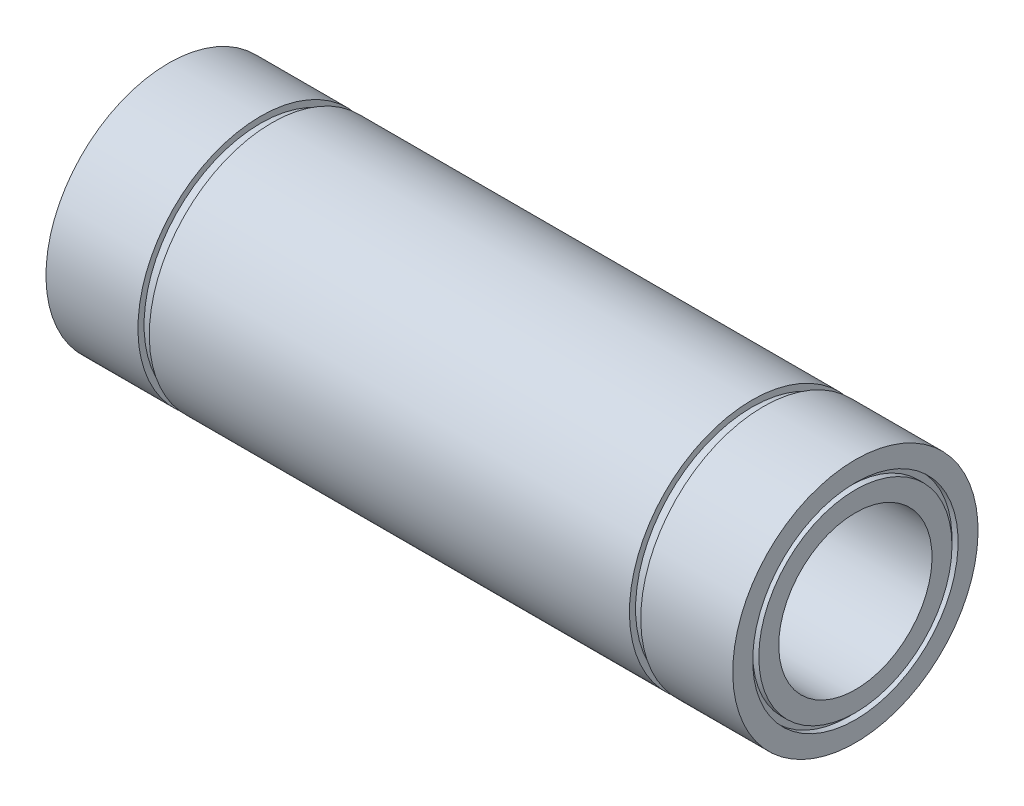
SolidWorks part; units mm, degrees
material "Ст3сп ГОСТ 535-2005"
ref_plane "Plano frontal" through (0, 0, 0) normal (0, 0, 1) x (1, 0, 0)
ref_plane "Plano superior" through (0, 0, 0) normal (0, 1, 0) x (1, 0, 0)
ref_plane "Plano direito" through (0, 0, 0) normal (1, 0, 0) x (0, 0, -1)
sketch "Esboço1" plane through (0, 0, 0) normal (0, 0, 1) x (1, 0, 0)
  line L0 (-56, 20) -> (-41, 20)
  line L1 (-41, 20) -> (-41, 19)
  line L2 (-41, 19) -> (-39.15, 19)
  line L3 (-39.15, 19) -> (-39.15, 20)
  line L4 (-39.15, 20) -> (39.15, 20)
  line L5 (39.15, 20) -> (39.15, 19)
  line L6 (39.15, 19) -> (41, 19)
  line L7 (41, 19) -> (41, 20)
  line L8 (41, 20) -> (56, 20)
  line L9 (56, 20) -> (56, 16.75)
  line L10 (56, 12.5) -> (-56, 12.5)
  line L11 (-56, 12.5) -> (-56, 15.75)
  line L12 (0, 12.5) -> (0, 0) construction
  line L13 (0, 0) -> (-86.5, 0) construction
  line L14 (-56, 16.75) -> (-56, 20)
  line L15 (-56, 16.75) -> (-55, 16.75)
  line L16 (56, 15.75) -> (56, 12.5)
  line L17 (-55, 16.75) -> (-55, 15.75)
  line L18 (-55, 15.75) -> (-56, 15.75)
  line L19 (56, 16.75) -> (55, 16.75)
  line L21 (56, 15.75) -> (55, 15.75)
  line L22 (55, 16.75) -> (55, 15.75)
  dimension "D1" = 112
  dimension "D2" = 82
  dimension "D3" = 1.85
  dimension "D4" = 25
  dimension "D5" = 40
  dimension "D6" = 38
  dimension "D7" = 1
  dimension "D8" = 1
  dimension "D9" = 1
  dimension "D10" = 1
revolve "Revolução1" add sketch "Esboço1" angle 360 about L13
